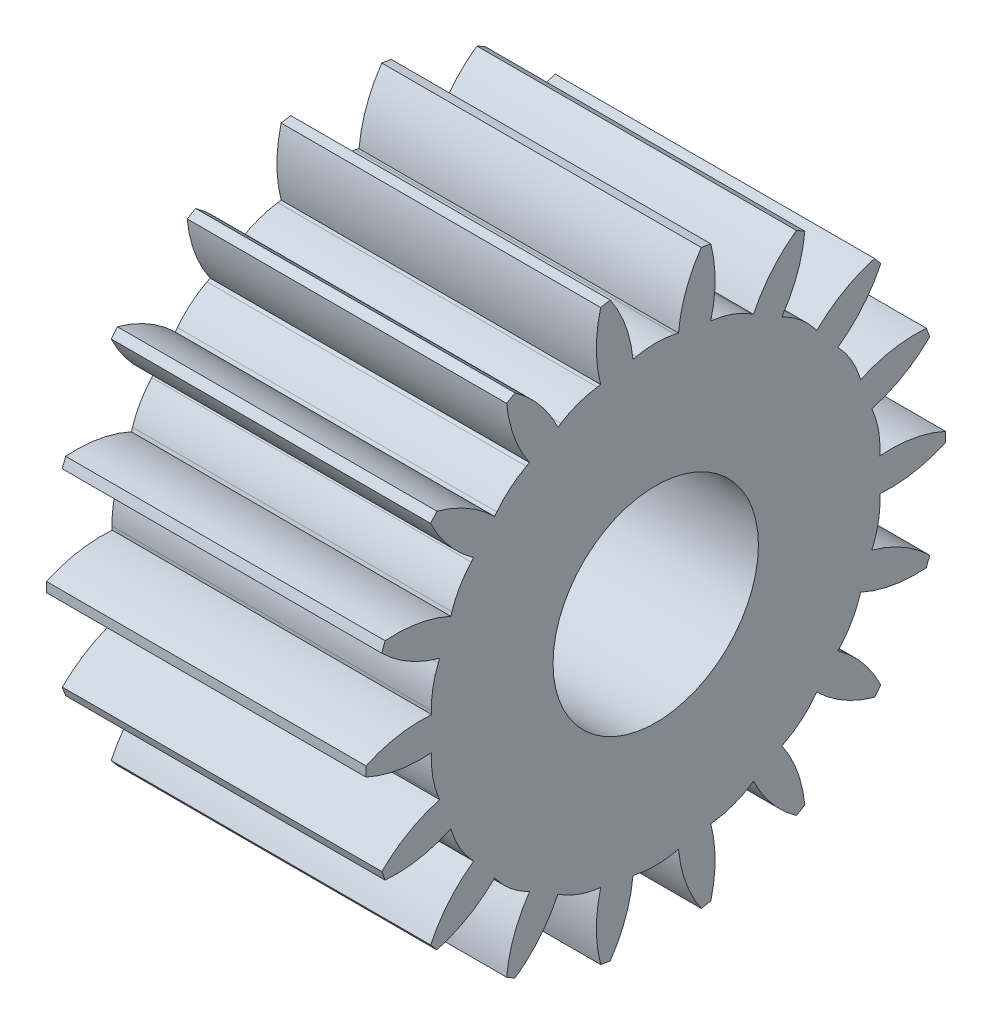
SolidWorks part; units mm, degrees
ref_plane "Front Plane" through (0, 0, 0) normal (0, 0, 1) x (1, 0, 0)
ref_plane "Top Plane" through (0, 0, 0) normal (0, 1, 0) x (1, 0, 0)
ref_plane "Right Plane" through (0, 0, 0) normal (1, 0, 0) x (0, 0, -1)
sketch "Sketch1" plane through (0, 0, 0) normal (1, 0, 0) x (0, 0, -1)
  circle A0 centre (0, 0) radius 63.5
  dimension "D1" = 127
extrude "Boss-Extrude1" add sketch "Sketch1" along normal mid plane 70
sketch "Sketch6" plane through (35, 0, 0) normal (1, 0, 0) x (0, 0, -1)
  circle A0 centre (0, 0) radius 22.5
  dimension "D1" = 45
extrude "Cut-Extrude4" cut sketch "Sketch6" against normal through all
sketch "Sketch7" plane through (35, 0, 0) normal (1, 0, 0) x (0, 0, -1)
  line L0 (0, 0) -> (0, 100.0792) construction
  line L1 (0, 50.0396) -> (-4.985, 48.9619)
  line L2 (0, 50.0396) -> (4.985, 48.9619)
  line L3 (-9.975, 62.7116) -> (0, 72.1676)
  line L4 (9.975, 62.7116) -> (0, 72.1676)
  circle A0 centre (0, 0) radius 49.215 construction
  circle A1 centre (0, 0) radius 57.15 construction
  arc A2 (-4.985, 48.9619) -> (-9.975, 62.7116) centre (-33.8085, 46.2817) ccw
  circle A3 centre (0, 0) radius 63.5 construction
  arc A4 (4.985, 48.9619) -> (9.975, 62.7116) centre (33.8085, 46.2817) cw
  dimension "D1" = 114.3
  dimension "D2" = 98.43
  dimension "D3" = 4.99
  dimension "D4" = 19.95
extrude "Cut-Extrude5" cut sketch "Sketch7" against normal through all
fillet "Fillet1" radius 20 1 edges at (0, 50.0396, 0)
pattern_circular "CirPattern3" count 18 over 360 about axis through (0, 0, 0) along (1, 0, 0) of "Cut-Extrude5", "Fillet1"
